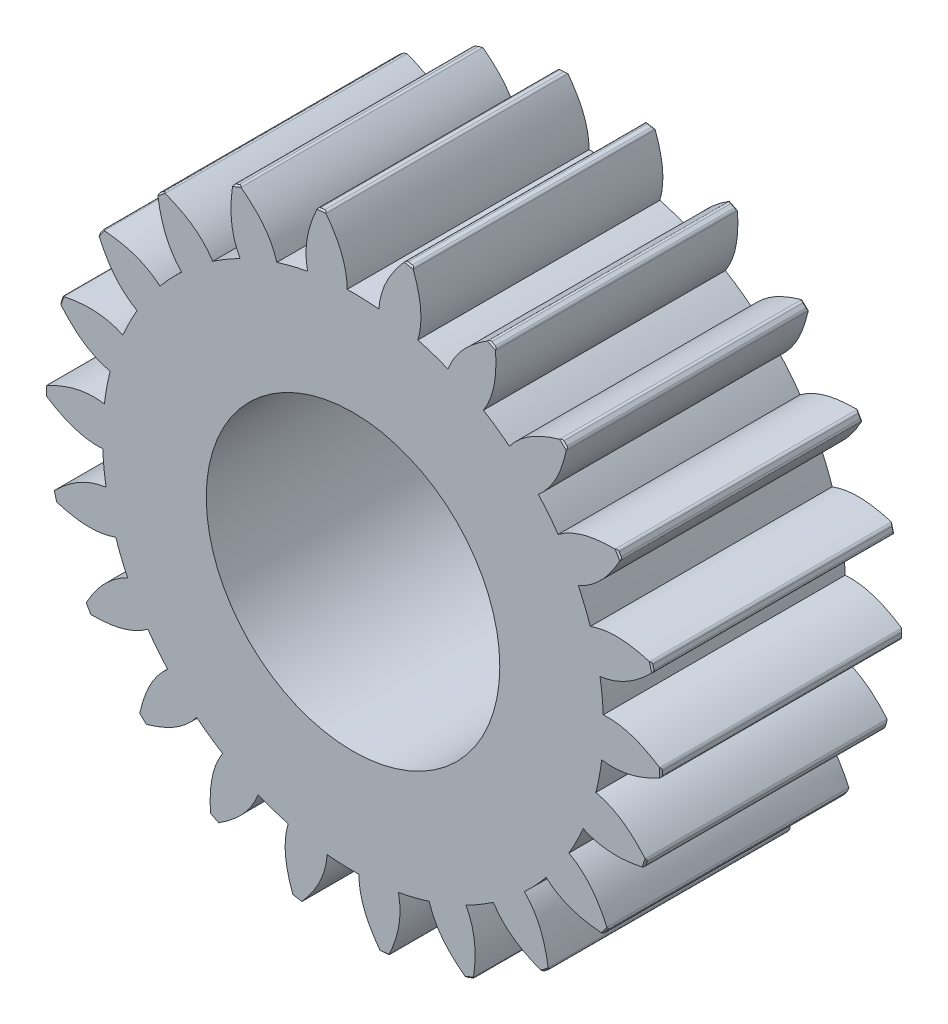
SolidWorks part; units mm, degrees
ref_plane "Front Plane" through (0, 0, 0) normal (0, 0, 1) x (1, 0, 0)
ref_plane "Top Plane" through (0, 0, 0) normal (0, 1, 0) x (1, 0, 0)
ref_plane "Right Plane" through (0, 0, 0) normal (1, 0, 0) x (0, 0, -1)
sketch "Sketch1" plane through (0, 0, 0) normal (0, 0, 1) x (1, 0, 0)
  line L0 (-430.4957, 0) -> (21094.2886, 0) construction
  line L1 (0, -430.4957) -> (0, 21094.2886) construction
  line L2 (0, 35.4633) -> (4.5838, 35.581) construction
  line L3 (4.5838, 35.581) -> (15.14, 32.5238)
  line L4 (15.14, 32.5238) -> (24.2754, 26.4144)
  line L5 (24.2754, 26.4144) -> (31.1327, 17.8261)
  line L6 (4.5838, 35.581) -> (-6.3161, 36.9852) construction
  line L7 (15.14, 32.5238) -> (-4.7867, 41.7998) construction
  line L8 (24.2754, 26.4144) -> (0, 48.7241) construction
  line L9 (31.1327, 17.8261) -> (9.2892, 55.9751) construction
  line L10 (0, 0) -> (-0.8753, 34.1138) construction
  line L11 (-6.4025, 35.2991) -> (-3.656, 35.3695) construction
  line L12 (-6.4025, 35.2991) -> (-3.656, 35.3695) construction
  line L13 (0, 0) -> (-3.656, 35.3695) construction
  circle A0 centre (0, 0) radius 34.125
  circle A1 centre (0, 0) radius 38.5 construction
  circle A2 centre (0, 0) radius 35.875
  arc A4 (-3.8122, 41.8266) -> (-4.8238, 41.7221) centre (0, 0) ccw
  spline S0 degree 3 poles (-6.1908, 33.5587) (-6.3173, 34.1421) (-6.4517, 35.2934) (-6.2957, 38.0828) (-5.5392, 40.2147) (-4.8238, 41.7221) knots -0.06375 -0.06375 -0.06375 -0.06375 0 0.062666 0.246998 0.246998 0.246998 0.246998
  spline S1 degree 3 poles (-0.8043, 34.1155) (-0.7954, 35.2991) (-1.3233, 38.0667) (-2.8036, 40.4974) (-3.8122, 41.8266) knots -0.06375 -0.06375 -0.06375 -0.06375 0.062666 0.246998 0.246998 0.246998 0.246998
  dimension "D2" = 77
  dimension "D3" = 71.75
  dimension "D4" = 68.25
  dimension "D5" = 10.99
  dimension "D6" = 10.99
  dimension "D7" = 21.98
  dimension "D8" = 32.97
  dimension "D9" = 43.96
extrude "Boss-Extrude2" add sketch "Sketch1" along normal blind 32.97 contours A2 S1 A4 S0 | A0 S1 A2 S0 | A0 A4
chamfer "Chamfer2" distance 0.2 angle 45 1 edges at (-4.3183, 41.7774, 32.97)
chamfer "Chamfer3" distance 0.2 angle 45 1 edges at (-4.3183, 41.7774, 0)
fillet "Fillet3" radius 0.4 2 edges at (-4.8238, 41.7221, 16.485) (-3.8122, 41.8266, 16.485)
pattern_circular "CirPattern20" count 22 over 360 about axis through (0, 0, 32.97) along (0, 0, 1) of "Boss-Extrude2", "Chamfer2", "Chamfer3", "Fillet3"
sketch "Sketch2" plane through (0, 0, 32.97) normal (0, 0, 1) x (1, 0, 0)
  circle A0 centre (0, 0) radius 20
  dimension "D1" = 40
extrude "Cut-Extrude1" cut sketch "Sketch2" against normal through all
